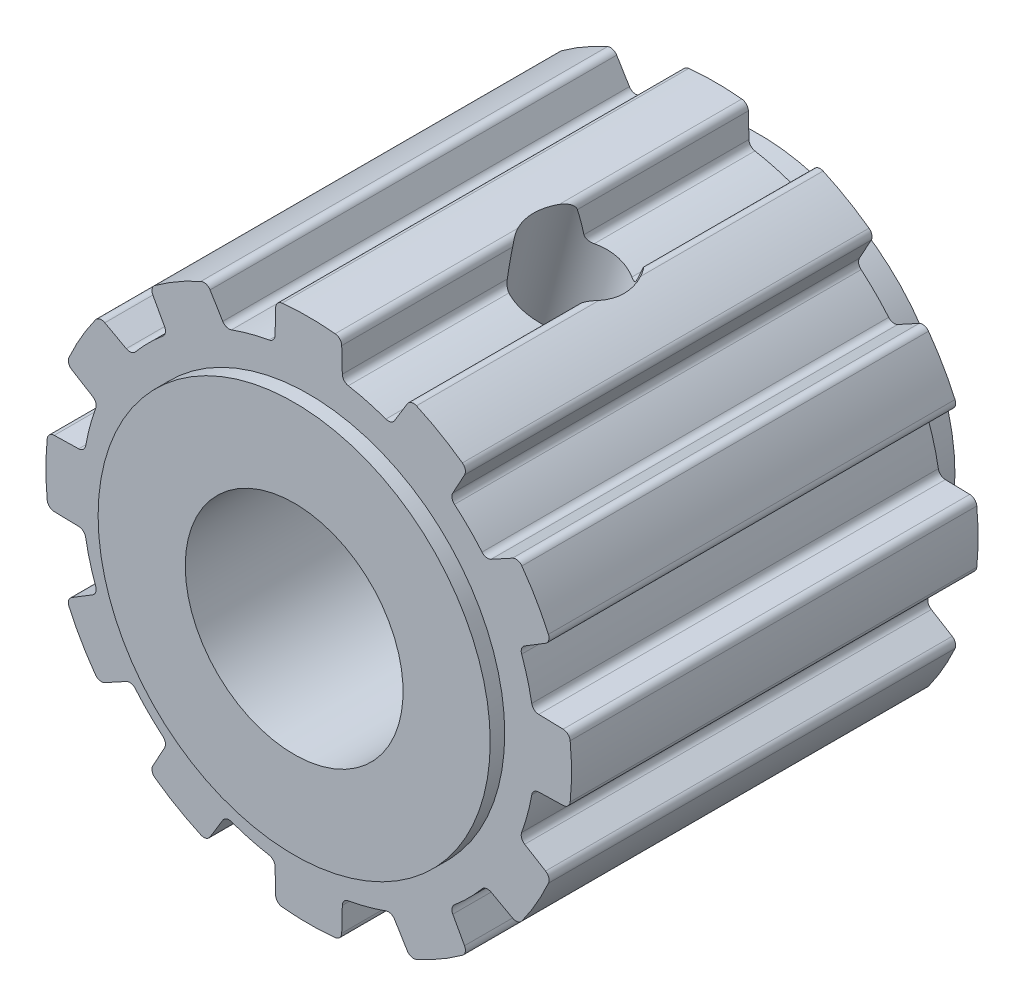
SolidWorks part; units mm, degrees
material "PW80:Mi:0:17:C1:0:1:2:Re:26:"
ref_plane "Plane1" through (0, 0, 0) normal (0, 0, 1) x (1, 0, 0)
ref_plane "Plane2" through (0, 0, 0) normal (0, 1, 0) x (1, 0, 0)
ref_plane "Plane3" through (0, 0, 0) normal (1, 0, 0) x (0, 0, -1)
sketch "Esquisse1" plane through (0, 0, 0) normal (0, 0, 1) x (1, 0, 0)
  line L0 (0, 0) -> (9.1163, 60.4788) construction
  line L1 (0, 0) -> (4.0372, 15.0671)
  line L2 (0, 0) -> (0, 70) construction
  line L3 (0, 18.0986) -> (0, 0)
  line L4 (0, 0) -> (7.9623, 63.1621) construction
  line L5 (2.315, 15.8385) -> (2.2742, 17.521)
  arc A0 (0, 18.0986) -> (1.8247, 18.0064) centre (0, 0) cw
  arc A1 (2.7274, 15.3583) -> (4.0372, 15.0671) centre (0, 0) cw
  arc A2 (2.7274, 15.3583) -> (2.315, 15.8385) centre (2.8148, 15.8506) cw
  arc A3 (1.8247, 18.0064) -> (2.2742, 17.521) centre (1.7743, 17.5089) cw
  point P13 (2.325, 15.4243)
  point P16 (2.2636, 17.9565)
  dimension "D1" = 18.0986
  dimension "D4" = 15.5986
  dimension "D6" = 0.5
  dimension "D2" = 15
  dimension "D3" = 6.428
  dimension "D5" = 7.185
extrude "Base-Extrusion" add sketch "Esquisse1" along normal blind 28
mirror "Bossage-Symétrie1"
mirror "Bossage-Symétrie2"
mirror "Bossage-Symétrie3"
mirror "Bossage-Symétrie4"
sketch "Esquisse2" plane through (0, 0, 28) normal (0, 0, 1) x (1, 0, 0)
  line L0 (0, 18.0986) -> (0, -18.0986)
  arc A0 (-1.8247, -18.0064) -> (1.8247, -18.0064) centre (0, 0) ccw construction
extrude "Enlèv. mat.-Extru.1" cut sketch "Esquisse2" against normal through all flip side to cut
mirror "Bossage-Symétrie5"
sketch "Esquisse3" plane through (0, 0, 28) normal (0, 0, 1) x (1, 0, 0)
  circle A0 centre (0, 0) radius 13.5
  arc A1 (10.5834, 14.6816) -> (7.4229, 16.5063) centre (0, 0) ccw construction
  dimension "D1" = 27
extrude "Boss.-Extru.1" add sketch "Esquisse3" along normal blind 1
sketch "Esquisse4" plane through (0, 0, 0) normal (0, 0, -1) x (-1, 0, 0)
  circle A0 centre (0, 0) radius 13.5
  dimension "D1" = 27
extrude "Boss.-Extru.2" add sketch "Esquisse4" along normal blind 3
sketch "Esquisse5" plane through (0, 0, -3) normal (0, 0, -1) x (-1, 0, 0)
  circle A0 centre (0, 0) radius 10
  dimension "D1" = 20
extrude "Boss.-Extru.3" add sketch "Esquisse5" along normal blind 2
sketch "Esquisse6" plane through (0, 0, -5) normal (0, 0, -1) x (-1, 0, 0)
  circle A0 centre (0, 0) radius 7.5
  circle A1 centre (0, 0) radius 10 construction
  dimension "D1" = 15
extrude "Enlèv. mat.-Extru.2" cut sketch "Esquisse6" against normal through all
ref_plane "Plan1" through (0, 0, 0) normal (0.2588, 0.9659, 0) x (-0.9659, 0.2588, 0)
sketch "Esquisse7" plane through (0, 0, 0) normal (0.2588, 0.9659, 0) x (-0.9659, 0.2588, 0)
  line L0 (0, 28) -> (0, 0) construction
  line L1 (2.8978, 0) -> (6.4229, 0) construction
  circle A0 centre (0, 14) radius 3.23
  dimension "D2" = 6.46
  dimension "D1" = 14
extrude "Enlèv. mat.-Extru.3" cut sketch "Esquisse7" along normal through all
equation "\"D4@Esquisse1\" = \"D1@Esquisse1\"-2.5"
equation "\"D3@Esquisse1\" = 360*(3.5/(\"D4@Esquisse1\"*2*pi*2))"
equation "\"D5@Esquisse1\" = 180*((10-3.5-(2*2.5*sin(20*pi/180))))/(12*10)"
equation "\"D2@Esquisse1\" = 360/(12*2)"
equation "\"D1@Esquisse1\" =( (10*12)/(2*pi))-1"
